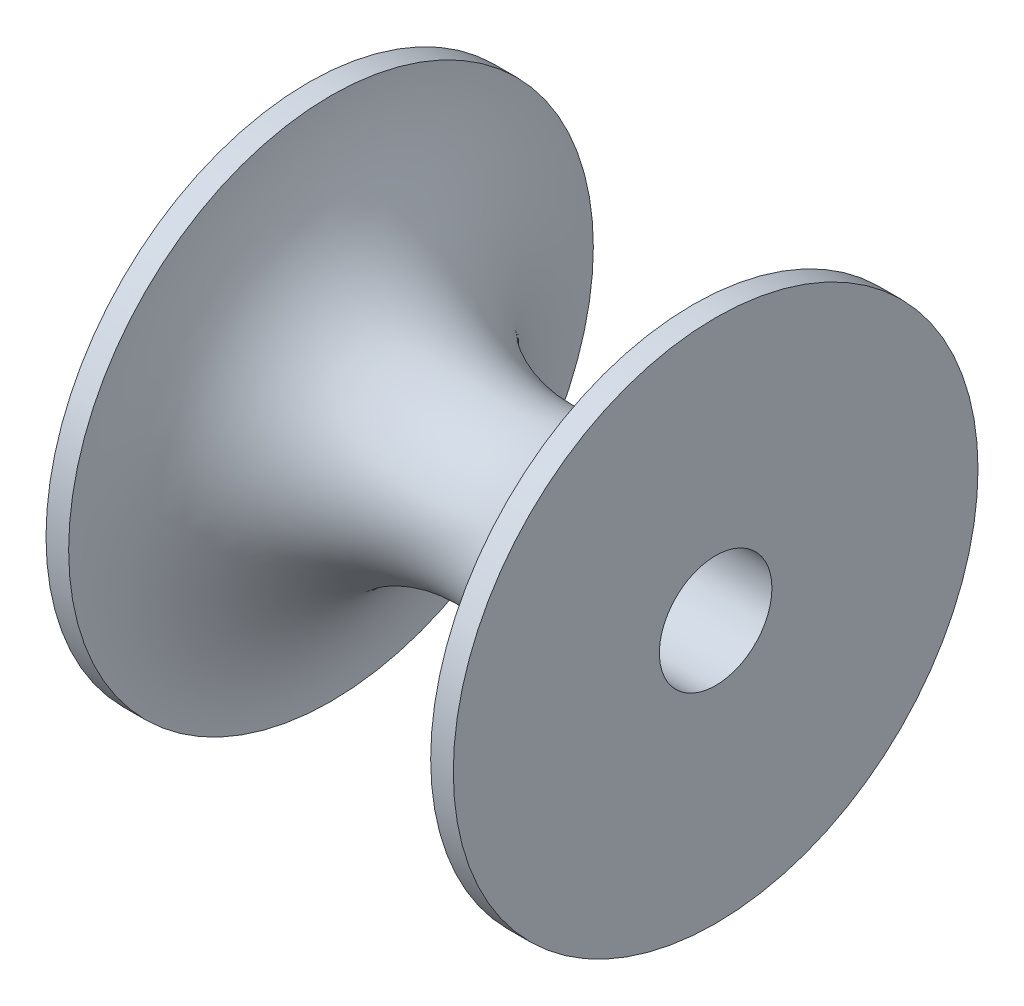
SolidWorks part; units mm, degrees
ref_plane "Front Plane" through (0, 0, 0) normal (0, 0, 1) x (1, 0, 0)
ref_plane "Top Plane" through (0, 0, 0) normal (0, 1, 0) x (1, 0, 0)
ref_plane "Right Plane" through (0, 0, 0) normal (1, 0, 0) x (0, 0, -1)
sketch "Sketch1" plane through (0, 0, 0) normal (0, 1, 0) x (1, 0, 0)
  line L0 (-16, 0) -> (-18, 0)
  line L1 (-18, 0) -> (-18, 23.19)
  line L2 (-18, 23.19) -> (18, 23.19)
  line L3 (18, 23.19) -> (18, 0)
  line L4 (18, 0) -> (16, 0)
  line L5 (-18, 16) -> (18, 16) construction
  line L6 (-18, 18) -> (18, 18) construction
  arc A0 (-16, 0) -> (16, 0) centre (0, 0) cw
  circle A1 centre (0, 0) radius 14.2875 construction
  dimension "D1" = 16
  dimension "D3" = 28.575
  dimension "D4" = 2
  dimension "D5" = 2
  dimension "D6" = 5.19
revolve "Revolve1" add sketch "Sketch1" angle 360 about L2
sketch "Sketch2" plane through (18, 0, 0) normal (1, 0, 0) x (0, 0, -1)
  circle A0 centre (23.19, 0) radius 4.975
  dimension "D1" = 9.95
extrude "Cut-Extrude1" cut sketch "Sketch2" against normal up to surface (36 mm away) up to face at (-18, 0, 0)
ref_plane "mid wheel" through (0, 0, 0) normal (1, 0, 0) x (0, 0, -1)
